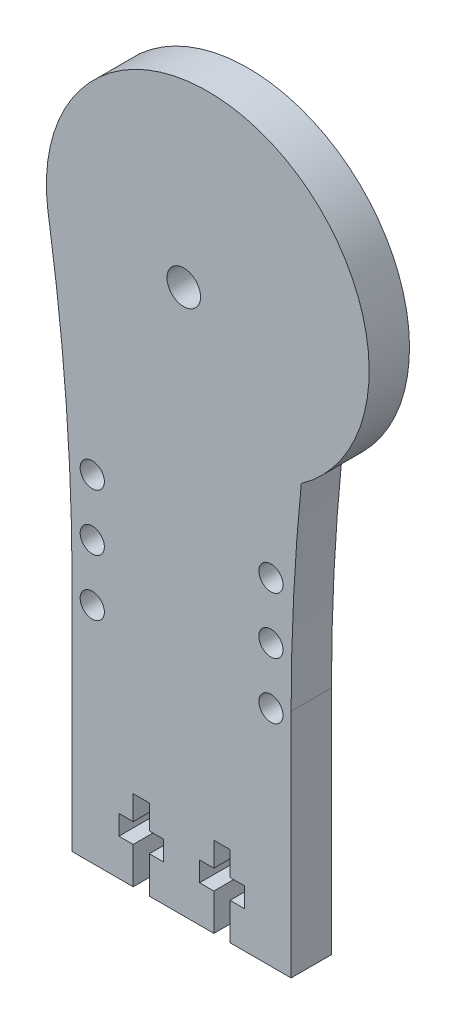
SolidWorks part; units mm, degrees
material "Acrílico (médio-alto impacto)"
ref_plane "Plano frontal" through (0, 0, 0) normal (0, 0, 1) x (1, 0, 0)
ref_plane "Plano superior" through (0, 0, 0) normal (0, 1, 0) x (1, 0, 0)
ref_plane "Plano direito" through (0, 0, 0) normal (1, 0, 0) x (0, 0, -1)
sketch "Esboço1" plane through (0, 0, 0) normal (0, 0, 1) x (1, 0, 0)
  line L0 (13.5691, 56.3389) -> (13.5691, 27.7156)
  line L1 (-13.5691, 56.3389) -> (-13.5691, 27.7156)
  line L2 (-16.3694, 93.6521) -> (-16.5765, 95.0244)
  arc A0 (13.5691, 27.7156) -> (-13.5691, 27.7156) centre (0, 38.1348) cw
  arc A1 (13.5691, 56.3389) -> (14.8299, 81.415) centre (263.5691, 56.3389) cw
  arc A2 (-13.5691, 56.3389) -> (-16.3694, 93.6521) centre (-263.5691, 56.3389) ccw
  arc A3 (14.8299, 81.415) -> (-16.4879, 94.4373) centre (3.2416, 97.7156) ccw
  dimension "D1" = 70
  dimension "D5" = 250
  dimension "D6" = 250
  dimension "D2" = 40
  dimension "D3" = 70
extrude "Ressalto-extrusão1" add sketch "Esboço1" along normal blind 5
sketch "Esboço4" plane through (0, 0, 5) normal (0, 0, 1) x (1, 0, 0)
  circle A0 centre (-4.6155, 109.78) radius 1.5
  circle A1 centre (5.3845, 109.78) radius 1.5
  circle A2 centre (-4.6155, 60) radius 1.5
  circle A3 centre (5.3845, 60) radius 1.5
  arc A4 (14.8299, 81.415) -> (13.5691, 56.3389) centre (263.5691, 56.3389) ccw construction
  point P11 (13.8845, 68.8928)
  dimension "D1" = 49.78
  dimension "D2" = 49.78
  dimension "D3" = 10
  dimension "D4" = 10
  dimension "D5" = 3
  dimension "D6" = 3
  dimension "D7" = 3
  dimension "D8" = 3
  dimension "D9" = 8.5
  dimension "D12" = 10
sketch "Esboço5" plane through (0, 0, 5) normal (0, 0, 1) x (1, 0, 0)
  line L1 (-9.6324, 105.19) -> (10.1676, 105.19)
  line L2 (-9.6324, 105.19) -> (-9.6324, 64.59)
  line L3 (-9.6324, 64.59) -> (10.1676, 64.59)
  line L4 (10.1676, 105.19) -> (10.1676, 64.59)
sketch "Esboço7" plane through (0, 0, 0) normal (0, 0, -1) x (-1, 0, 0)
  line L0 (-10.1676, 105.19) -> (-10.1676, 64.59) construction
  circle A0 centre (-0.2676, 95.19) radius 2.0767
  circle A1 centre (-5.3845, 109.78) radius 1.5 construction
  dimension "D1" = 14.59
  dimension "D2" = 9.9
extrude "Corte-extrusão5" cut sketch "Esboço7" against normal through all
sketch "Esboço8" plane through (0, 0, 5) normal (0, 0, 1) x (1, 0, 0)
  line L1 (13.5691, 27.7156) -> (-23.0263, 27.7156)
  line L2 (13.5691, 27.7156) -> (13.5691, 19.4405)
  line L3 (13.5691, 19.4405) -> (-23.0263, 19.4405)
  line L4 (-23.0263, 27.7156) -> (-23.0263, 19.4405)
extrude "Corte-extrusão6" cut sketch "Esboço8" against normal blind 10
sketch "Esboço9" plane through (0, 0, 5) normal (0, 0, 1) x (1, 0, 0)
  circle A0 centre (11.0676, 62.41) radius 1.5
  circle A1 centre (11.0676, 55.41) radius 1.5
  circle A2 centre (11.0676, 69.41) radius 1.5
  circle A3 centre (0.2676, 95.19) radius 2.0767 construction
  circle A4 centre (-11.0724, 55.41) radius 1.5
  circle A5 centre (-11.0724, 62.41) radius 1.5
  circle A6 centre (-11.0724, 69.41) radius 1.5
  dimension "D1" = 3
  dimension "D2" = 25.78
  dimension "D3" = 10.8
  dimension "D4" = 7
  dimension "D5" = 7
  dimension "D6" = 3
  dimension "D7" = 3
  dimension "D8" = 10.8
  dimension "D9" = 10.8
  dimension "D10" = 22.14
  dimension "D11" = 22.14
  dimension "D12" = 22.14
  dimension "D13" = 25.78
  dimension "D14" = 7
  dimension "D15" = 7
  dimension "D16" = 3
  dimension "D17" = 3
  dimension "D18" = 3
extrude "Corte-extrusão7" cut sketch "Esboço9" against normal through all
sketch "Esboço10" plane through (0, 0, 5) normal (0, 0, 1) x (1, 0, 0)
  line L0 (13.5691, 27.7156) -> (-13.5691, 27.7156) construction
  line L1 (5.9991, 27.7156) -> (3.9991, 27.7156)
  line L2 (5.9991, 27.7156) -> (5.9991, 32.2656)
  line L3 (5.9991, 37.7156) -> (3.9991, 37.7156)
  line L4 (3.9991, 27.7156) -> (3.9991, 32.2656)
  line L5 (3.9991, 34.7156) -> (3.9991, 37.7156)
  line L6 (-3.9991, 27.7156) -> (-5.9991, 27.7156)
  line L7 (-3.9991, 27.7156) -> (-3.9991, 32.2656)
  line L8 (-3.9991, 37.7156) -> (-5.9991, 37.7156)
  line L9 (-5.9991, 27.7156) -> (-5.9991, 32.2656)
  line L10 (-13.5691, 56.3389) -> (-13.5691, 27.7156) construction
  line L11 (13.5691, 56.3389) -> (13.5691, 27.7156) construction
  line L12 (3.9991, 32.2656) -> (2.2291, 32.2656)
  line L13 (7.7691, 32.2656) -> (5.9991, 32.2656)
  line L14 (7.7691, 32.2656) -> (7.7691, 34.7156)
  line L15 (7.7691, 34.7156) -> (5.9991, 34.7156)
  line L16 (2.2291, 32.2656) -> (2.2291, 34.7156)
  line L17 (-2.2291, 32.2656) -> (-3.9991, 32.2656)
  line L18 (-2.2291, 32.2656) -> (-2.2291, 34.7156)
  line L19 (-2.2291, 34.7156) -> (-3.9991, 34.7156)
  line L20 (-7.7691, 32.2656) -> (-7.7691, 34.7156)
  line L21 (3.9991, 34.7156) -> (2.2291, 34.7156)
  line L22 (-5.9991, 34.7156) -> (-7.7691, 34.7156)
  line L23 (-3.9991, 34.7156) -> (-3.9991, 37.7156)
  line L24 (-5.9991, 34.7156) -> (-5.9991, 37.7156)
  line L25 (-5.9991, 32.2656) -> (-7.7691, 32.2656)
  line L26 (5.9991, 34.7156) -> (5.9991, 37.7156)
  dimension "D1" = 2
  dimension "D2" = 2
  dimension "D3" = 7.57
  dimension "D4" = 7.57
  dimension "D5" = 4.55
  dimension "D6" = 4.55
  dimension "D7" = 2.45
  dimension "D8" = 2.45
  dimension "D9" = 10
  dimension "D10" = 10
  dimension "D11" = 1.77
  dimension "D12" = 1.77
  dimension "D13" = 1.77
  dimension "D14" = 1.77
extrude "Corte-extrusão8" cut sketch "Esboço10" against normal through all
